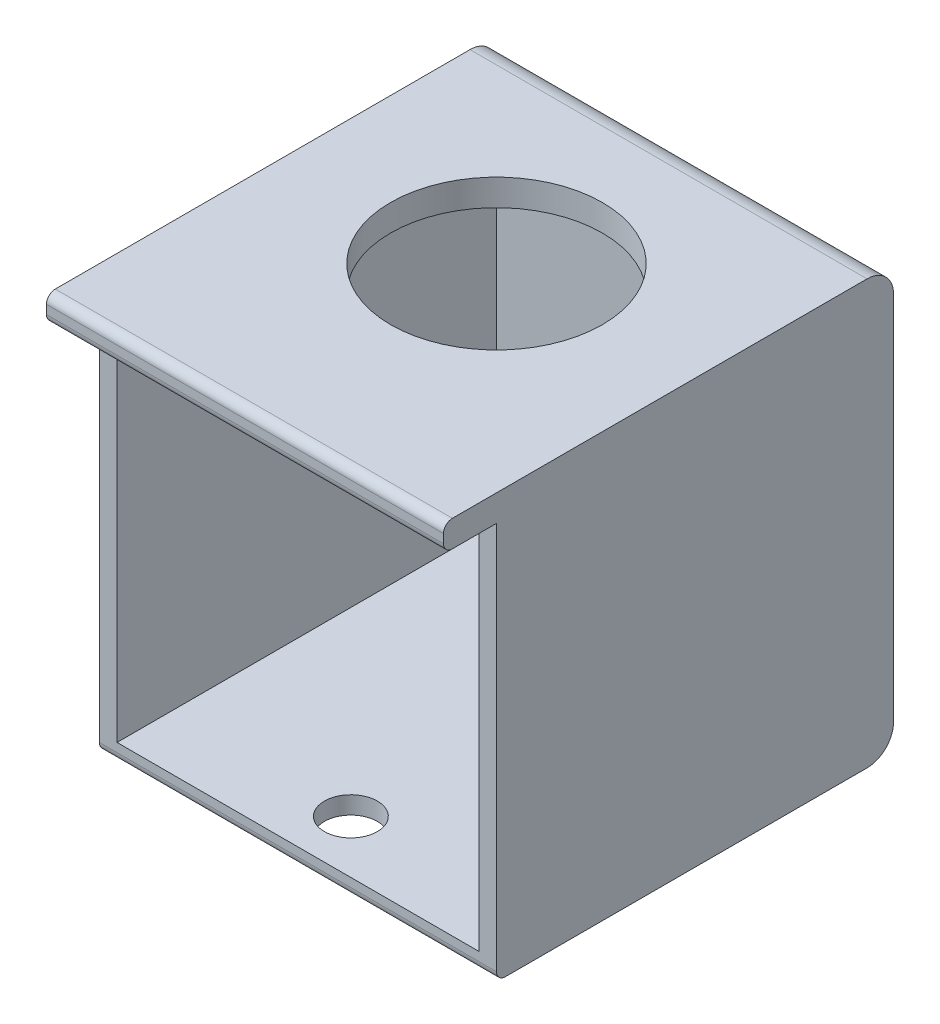
SolidWorks part; units mm, degrees
ref_plane "Спереди" through (0, 0, 0) normal (0, 0, 1) x (1, 0, 0)
ref_plane "Сверху" through (0, 0, 0) normal (0, 1, 0) x (1, 0, 0)
ref_plane "Справа" through (0, 0, 0) normal (1, 0, 0) x (0, 0, -1)
other "Configuration Table"
sketch "Эскиз1" plane through (0, 0, 0) normal (0, 1, 0) x (1, 0, 0)
  line L1 (-22.5, 22.5) -> (22.5, 22.5)
  line L2 (-22.5, 22.5) -> (-22.5, -22.5)
  line L3 (-22.5, -22.5) -> (22.5, -22.5)
  line L4 (22.5, 22.5) -> (22.5, -22.5)
  line L5 (0, -22.5) -> (0, 22.5) construction
  line L6 (-22.5, 0) -> (22.5, 0) construction
  point P0 (0, 0)
  dimension "D1" = 45
  dimension "D2" = 45
extrude "Бобышка-Вытянуть1" add sketch "Эскиз1" along normal blind 3
sketch "Эскиз2" plane through (0, 3, 0) normal (0, 1, 0) x (1, 0, 0)
  circle A0 centre (0, 0) radius 12
extrude "Вырез-Вытянуть1" cut sketch "Эскиз2" against normal blind 3
sketch "Эскиз3" plane through (0, 0, 0) normal (0, -1, 0) x (1, 0, 0)
  line L0 (22.5, -22.5) -> (-22.5, -22.5) construction
  line L1 (-22.5, 22.5) -> (-20.5, 22.5)
  line L2 (-22.5, 22.5) -> (-22.5, -22.5)
  line L3 (-22.5, -22.5) -> (-20.5, -22.5)
  line L4 (-20.5, 22.5) -> (-20.5, -22.5)
  line L5 (-21.5, -22.5) -> (-21.5, 22.5) construction
  line L6 (-22.5, 0) -> (-20.5, 0) construction
  point P380 (-21.5, 0)
  dimension "D1" = 2
extrude "Бобышка-Вытянуть3" add sketch "Эскиз3" along normal blind 45
ref_plane "Плоскость1" through (0, 0, 0) normal (-1, 0, 0) x (0, 0, 1)
mirror "Зеркальное отражение3" about plane through (0, 0, 0) normal (-1, 0, 0) of "Бобышка-Вытянуть1", "Бобышка-Вытянуть3"
sketch "Эскиз4" plane through (0, 3, 0) normal (0, 1, 0) x (1, 0, 0)
  circle A0 centre (0, 0) radius 12
extrude "Вырез-Вытянуть2" cut sketch "Эскиз4" against normal blind 3
sketch "Эскиз5" plane through (0, 0, 0) normal (0, -1, 0) x (1, 0, 0)
  line L0 (20.5, -22.5) -> (20.5, 22.5) construction
  line L1 (-20.5, -22.5) -> (20.5, -22.5)
  line L2 (-20.5, -22.5) -> (-20.5, -20.5)
  line L3 (-20.5, -20.5) -> (20.5, -20.5)
  line L4 (20.5, -22.5) -> (20.5, -20.5)
  line L5 (0, -20.5) -> (0, -22.5) construction
  line L6 (-20.5, -21.5) -> (20.5, -21.5) construction
  point P296 (0, -21.5)
  dimension "D1" = 2
extrude "Бобышка-Вытянуть4" add sketch "Эскиз5" along normal blind 45
sketch "Эскиз6" plane through (0, 0, -20.5) normal (0, 0, 1) x (1, 0, 0)
  line L0 (20.5, -45) -> (20.5, 0) construction
  line L1 (-20.5, -45) -> (20.5, -45)
  line L2 (-20.5, -45) -> (-20.5, -43)
  line L3 (-20.5, -43) -> (20.5, -43)
  line L4 (20.5, -45) -> (20.5, -43)
  line L5 (0, -43) -> (0, -45) construction
  line L6 (-20.5, -44) -> (20.5, -44) construction
  point P512 (0, -44)
  dimension "D1" = 2
extrude "Бобышка-Вытянуть5" add sketch "Эскиз6" along normal blind 43
sketch "Эскиз8" plane through (0, 0, 22.5) normal (0, 0, 1) x (1, 0, 0)
  line L0 (22.5, 3) -> (22.5, -45) construction
  line L1 (-22.5, 3) -> (22.5, 3)
  line L2 (-22.5, 3) -> (-22.5, 0)
  line L3 (-22.5, 0) -> (22.5, 0)
  line L4 (22.5, 3) -> (22.5, 0)
  line L5 (0, 0) -> (0, 3) construction
  line L6 (-22.5, 1.5) -> (22.5, 1.5) construction
  point P504 (0, 1.5)
extrude "Бобышка-Вытянуть6" add sketch "Эскиз8" along normal blind 6
fillet "Скругление3" radius 1 2 edges at (0, 0, 28.5) (0, 3, 28.5)
fillet "Скругление4" radius 3 2 edges at (0, -45, -22.5) (0, 3, -22.5)
sketch "Эскиз9" plane through (0, -45, 0) normal (0, -1, 0) x (1, 0, 0)
  line L0 (0, 26.4) -> (0, -26.4) construction
  line L1 (-3, 16.5) -> (3.6741, 16.5)
  line L2 (22.5, 22.5) -> (-22.5, 22.5) construction
  circle A0 centre (0, 16.5) radius 3
  dimension "D1" = 6
extrude "Вырез-Вытянуть3" cut sketch "Эскиз9" against normal blind 2 contours A0
fillet "Скругление8" radius 1 1 edges at (0, -45, 22.5)
